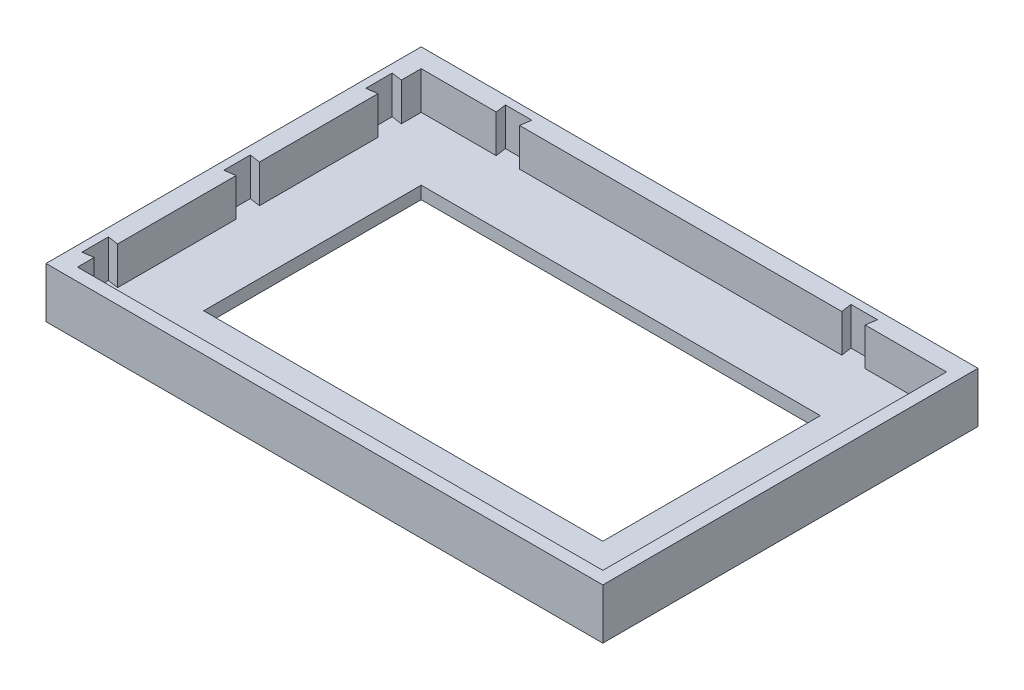
SolidWorks part; units mm, degrees
ref_plane "Front Plane" through (0, 0, 0) normal (0, 0, 1) x (1, 0, 0)
ref_plane "Top Plane" through (0, 0, 0) normal (0, 1, 0) x (1, 0, 0)
ref_plane "Right Plane" through (0, 0, 0) normal (1, 0, 0) x (0, 0, -1)
sketch "Sketch1" plane through (0, 0, 0) normal (0, 1, 0) x (1, 0, 0)
  line L1 (-38.2233, -34.0464) -> (50.0767, -34.0464)
  line L2 (-38.2233, -34.0464) -> (-38.2233, 25.4536)
  line L3 (-38.2233, 25.4536) -> (50.0767, 25.4536)
  line L4 (50.0767, -34.0464) -> (50.0767, 25.4536)
  dimension "D1" = 88.3
  dimension "D2" = 59.5
extrude "Boss-Extrude1" add sketch "Sketch1" along normal blind 8
sketch "Sketch2" plane through (0, 8, 0) normal (0, 1, 0) x (1, 0, 0)
  line L0 (50.0767, 25.4536) -> (-38.2233, 25.4536) construction
  line L1 (-35.2233, -32.0464) -> (48.0767, -32.0464)
  line L2 (-35.2233, -32.0464) -> (-35.2233, 22.4536)
  line L3 (-35.2233, 22.4536) -> (48.0767, 22.4536)
  line L4 (48.0767, -32.0464) -> (48.0767, 22.4536)
  line L5 (-38.2233, -34.0464) -> (50.0767, -34.0464) construction
  line L6 (-38.2233, 25.4536) -> (-38.2233, -34.0464) construction
  line L7 (50.0767, -34.0464) -> (50.0767, 25.4536) construction
  dimension "D1" = 3
  dimension "D2" = 2
  dimension "D3" = 3
  dimension "D4" = 2
extrude "Cut-Extrude1" cut sketch "Sketch2" against normal offset from surface (6 mm away) 2 up to face at (5.9267, 0, 4.2964)
sketch "Sketch3" plane through (0, 8, 0) normal (0, 1, 0) x (1, 0, 0)
  line L0 (-35.2233, -29.3964) -> (-36.9233, -29.6464)
  line L1 (-35.2233, 22.4536) -> (-35.2233, -32.0464) construction
  line L2 (-36.9233, -29.6464) -> (-36.9233, -25.4464)
  line L3 (-36.9233, -25.4464) -> (-35.2233, -25.6964)
  line L4 (-35.2233, 22.4536) -> (-35.2233, -32.0464) construction
  line L5 (-35.2233, -25.6964) -> (-35.2233, -29.3964)
  line L6 (-35.2233, -32.0464) -> (48.0767, -32.0464) construction
  line L7 (-35.2233, -6.8964) -> (-36.9233, -7.1464)
  line L8 (-36.9233, -7.1464) -> (-36.9233, -2.9464)
  line L9 (-36.9233, -2.9464) -> (-35.2233, -3.1964)
  line L10 (-35.2233, -3.1964) -> (-35.2233, -6.8964)
  line L11 (-35.2233, 15.6036) -> (-36.9233, 15.3536)
  line L12 (-36.9233, 15.3536) -> (-36.9233, 19.5536)
  line L13 (-36.9233, 19.5536) -> (-35.2233, 19.3036)
  line L14 (-35.2233, 19.3036) -> (-35.2233, 15.6036)
  line L15 (-35.2233, -29.3964) -> (-35.2233, -6.8964) construction
  line L16 (35.1767, 22.4536) -> (31.4767, 22.4536)
  line L17 (48.0767, 22.4536) -> (-35.2233, 22.4536) construction
  line L18 (-23.3233, 22.4536) -> (-23.5733, 24.1536)
  line L19 (-23.5733, 24.1536) -> (-19.3733, 24.1536)
  line L20 (-19.3733, 24.1536) -> (-19.6233, 22.4536)
  line L21 (48.0767, 22.4536) -> (-35.2233, 22.4536) construction
  line L22 (-19.6233, 22.4536) -> (-23.3233, 22.4536)
  line L23 (31.4767, 22.4536) -> (31.2267, 24.1536)
  line L24 (31.2267, 24.1536) -> (35.4267, 24.1536)
  line L25 (35.4267, 24.1536) -> (35.1767, 22.4536)
  line L26 (-19.6233, 22.4536) -> (35.1767, 22.4536) construction
  point P9 (-36.9233, -27.5464)
  point P10 (-35.2233, -27.5464)
  point P28 (-21.4733, 22.4536)
  point P32 (-21.4733, 24.1536)
  dimension "D1" = 4.2
  dimension "D2" = 1.7
  dimension "D3" = 3.7
  dimension "D4" = 4.5
  dimension "D6" = 22.5
  dimension "D7" = 4.2
  dimension "D8" = 1.7
  dimension "D9" = 13.75
  dimension "D10" = 3.7
  dimension "D12" = 54.8
  dimension "D5" = 3
  dimension "D11" = 2
extrude "Cut-Extrude2" cut sketch "Sketch3" against normal up to surface (6 mm away) up to face at (6.4267, 2, 4.7964)
sketch "Sketch4" plane through (0, 2, 0) normal (0, 1, 0) x (1, 0, 0)
  line L0 (-35.2233, 15.6036) -> (-35.2233, -3.1964) construction
  line L1 (-25.2233, -22.0464) -> (38.0767, -22.0464)
  line L2 (-25.2233, -22.0464) -> (-25.2233, 12.4536)
  line L3 (-25.2233, 12.4536) -> (38.0767, 12.4536)
  line L4 (38.0767, -22.0464) -> (38.0767, 12.4536)
  line L5 (31.4767, 22.4536) -> (-19.6233, 22.4536) construction
  line L6 (48.0767, -32.0464) -> (48.0767, 22.4536) construction
  line L7 (-35.2233, -32.0464) -> (48.0767, -32.0464) construction
  dimension "D1" = 10
  dimension "D2" = 10
  dimension "D3" = 10
  dimension "D4" = 10
extrude "Cut-Extrude3" cut sketch "Sketch4" against normal through all
